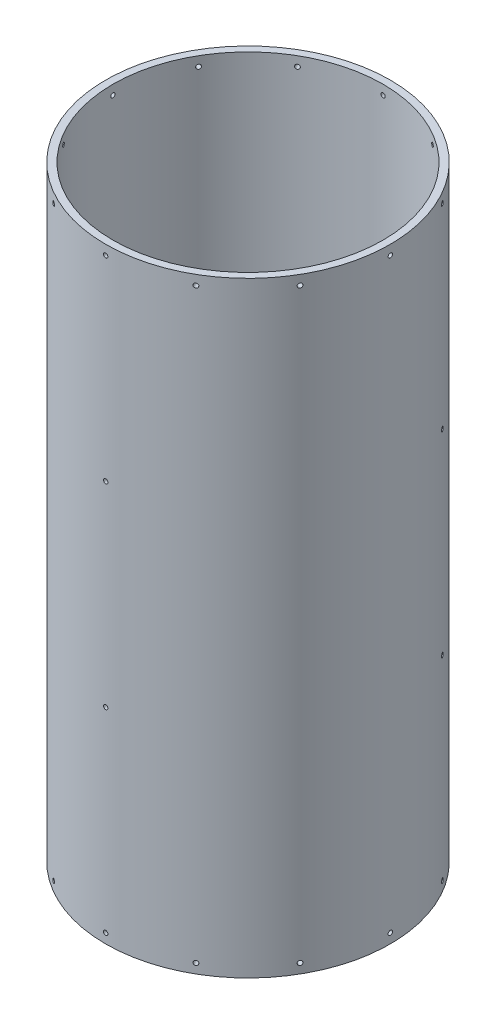
SolidWorks part; units mm, degrees
material "PVC Rigid"
ref_plane "Front Plane" through (0, 0, 0) normal (0, 0, 1) x (1, 0, 0)
ref_plane "Top Plane" through (0, 0, 0) normal (0, 1, 0) x (1, 0, 0)
ref_plane "Right Plane" through (0, 0, 0) normal (1, 0, 0) x (0, 0, -1)
sketch "Sketch1" plane through (0, 0, 0) normal (0, 1, 0) x (1, 0, 0)
  circle A0 centre (0, 0) radius 93.6625
  circle A1 centre (0, 0) radius 88.9
  dimension "D1" = 187.325
  dimension "D2" = 177.8
extrude "Boss-Extrude1" add sketch "Sketch1" along normal mid plane 398.78
ref_plane "Plane1" through (0, 0, 93.6625) normal (0, 0, 1) x (1, 0, 0)
sketch "Sketch3" plane through (0, 0, 93.6625) normal (0, 0, 1) x (1, 0, 0)
  line L0 (0, -103.0288) -> (0, 103.0288) construction
  line L1 (-93.6625, -199.39) -> (93.6625, -199.39) construction
  circle A0 centre (0, -193.04) radius 1.4351
  dimension "D1" = 2.8702
  dimension "D2" = 6.35
extrude "Cut-Extrude1" cut sketch "Sketch3" against normal blind 19.304
pattern_circular "CirPattern1" count 12 over 360 about axis through (0, 199.39, 0) along (0, -1, 0) of "Cut-Extrude1"
mirror "Mirror1" about plane through (0, 0, 0) normal (0, 1, 0) of "CirPattern1", "Cut-Extrude1"
sketch "Sketch4" plane through (0, 0, 93.6625) normal (0, 0, 1) x (1, 0, 0)
  line L0 (0, -103.0288) -> (0, 103.0288) construction
  circle A0 centre (0, 64.3636) radius 1.4351
  circle A1 centre (0, -64.3636) radius 1.4351
  circle A2 centre (0, 193.04) radius 1.4351 construction
  circle A3 centre (0, -193.04) radius 1.4351 construction
  dimension "D1" = 128.6764
  dimension "D2" = 128.6764
  dimension "D3" = 2.8702
  dimension "D4" = 2.8702
extrude "Cut-Extrude2" cut sketch "Sketch4" against normal blind 43.18
pattern_circular "CirPattern2" count 3 over 360 about axis through (0, 199.39, 0) along (0, -1, 0) of "Cut-Extrude2"
